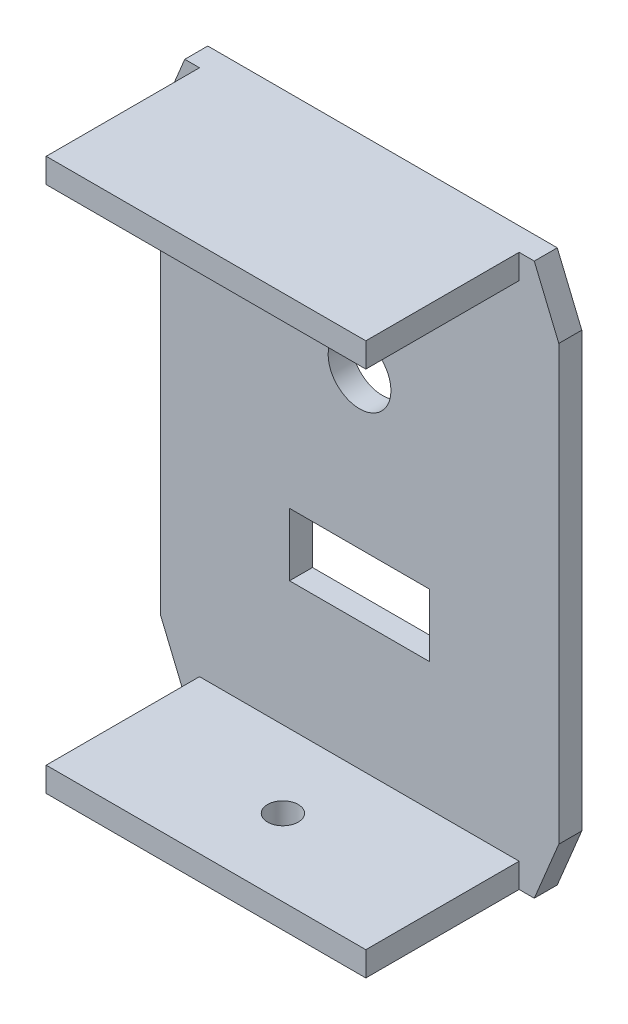
SolidWorks part; units mm, degrees
ref_plane "Front Plane" through (0, 0, 0) normal (0, 0, 1) x (1, 0, 0)
ref_plane "Top Plane" through (0, 0, 0) normal (0, 1, 0) x (1, 0, 0)
ref_plane "Right Plane" through (0, 0, 0) normal (1, 0, 0) x (0, 0, -1)
sketch "Sketch1" plane through (0, 0, 0) normal (0, 0, 1) x (1, 0, 0)
  line L0 (25.1428, 48.3492) -> (30.2228, 36.1136)
  line L1 (-52.3272, 48.3492) -> (30.2228, 48.3492)
  line L2 (-52.3272, 48.3492) -> (-52.3272, -65.9508)
  line L3 (-52.3272, -65.9508) -> (30.2228, -65.9508)
  line L4 (30.2228, 48.3492) -> (30.2228, -65.9508)
  line L5 (-52.3272, 48.3492) -> (30.2228, -65.9508) construction
  line L6 (-52.3272, -65.9508) -> (30.2228, 48.3492) construction
  line L7 (-11.0522, 24.671) -> (-11.0522, -30.9925) construction
  line L8 (-37.0997, -8.8008) -> (9.9758, -8.8008) construction
  line L9 (-47.2472, 48.3492) -> (-52.3272, 36.1136)
  line L10 (25.1428, -65.9508) -> (30.2228, -53.7152)
  line L11 (-47.2472, -65.9508) -> (-52.3272, -53.7152)
  point P0 (-11.0522, -8.8008)
extrude "Boss-Extrude1" add sketch "Sketch1" along normal blind 4.7625 contours L11 L3 L10 L4 L0 L1 L9 L2
sketch "Sketch3" plane through (0, 0, 4.7625) normal (0, 0, 1) x (1, 0, 0)
  line L0 (-44.1992, 43.2694) -> (22.0017, 43.2694)
  line L1 (-44.1992, 43.2694) -> (-44.1992, 48.3492)
  line L2 (-44.1992, 48.3492) -> (22.0017, 48.3492)
  line L3 (22.0017, 43.2694) -> (22.0017, 48.3492)
  line L4 (-47.2472, 48.3492) -> (25.1428, 48.3492) construction
  line L5 (-68.3673, -8.8008) -> (63.7578, -8.8008) construction
  line L6 (22.0017, -60.871) -> (22.0017, -65.9508)
  line L7 (-44.1992, -60.871) -> (22.0017, -60.871)
  line L8 (-44.1992, -60.871) -> (-44.1992, -65.9508)
  line L9 (-44.1992, -65.9508) -> (22.0017, -65.9508)
  dimension "D1" = 3.048
  dimension "D2" = 0
  dimension "D3" = 66.2009
extrude "Boss-Extrude2" add sketch "Sketch3" along normal blind 31.75
sketch "Sketch4" plane through (0, 0, 0) normal (0, 0, -1) x (-1, 0, 0)
  line L0 (11.0522, -17.5806) -> (11.0522, -65.9508) construction
  line L1 (47.2472, -65.9508) -> (-25.1428, -65.9508) construction
  line L2 (-24.5371, -27.8508) -> (43.3344, -27.8508) construction
  line L4 (-3.4478, -21.3508) -> (25.5522, -21.3508)
  line L5 (-3.4478, -21.3508) -> (-3.4478, -34.3508)
  line L6 (-3.4478, -34.3508) -> (25.5522, -34.3508)
  line L7 (25.5522, -21.3508) -> (25.5522, -34.3508)
  line L8 (-3.4478, -21.3508) -> (25.5522, -34.3508) construction
  line L9 (-3.4478, -34.3508) -> (25.5522, -21.3508) construction
  point P6 (11.0522, -27.8508)
  dimension "D1" = 38.1
  dimension "D2" = 28.9999
  dimension "D3" = 13
extrude "Cut-Extrude1" cut sketch "Sketch4" against normal blind 4.7625
sketch "Sketch5" plane through (0, 0, 0) normal (0, 0, -1) x (-1, 0, 0)
  line L0 (47.2472, 48.3492) -> (-25.1428, 48.3492) construction
  circle A0 centre (11.0522, 10.2492) radius 6.5
  dimension "D1" = 13
  dimension "D2" = 38.1
extrude "Cut-Extrude2" cut sketch "Sketch5" against normal blind 4.7625
sketch "Sketch6" plane through (0, -65.9508, 0) normal (0, -1, 0) x (1, 0, 0)
  circle A0 centre (-11.0522, 20.6375) radius 3.175
  dimension "D1" = 6.35
extrude "Cut-Extrude3" cut sketch "Sketch6" against normal blind 7.3025
